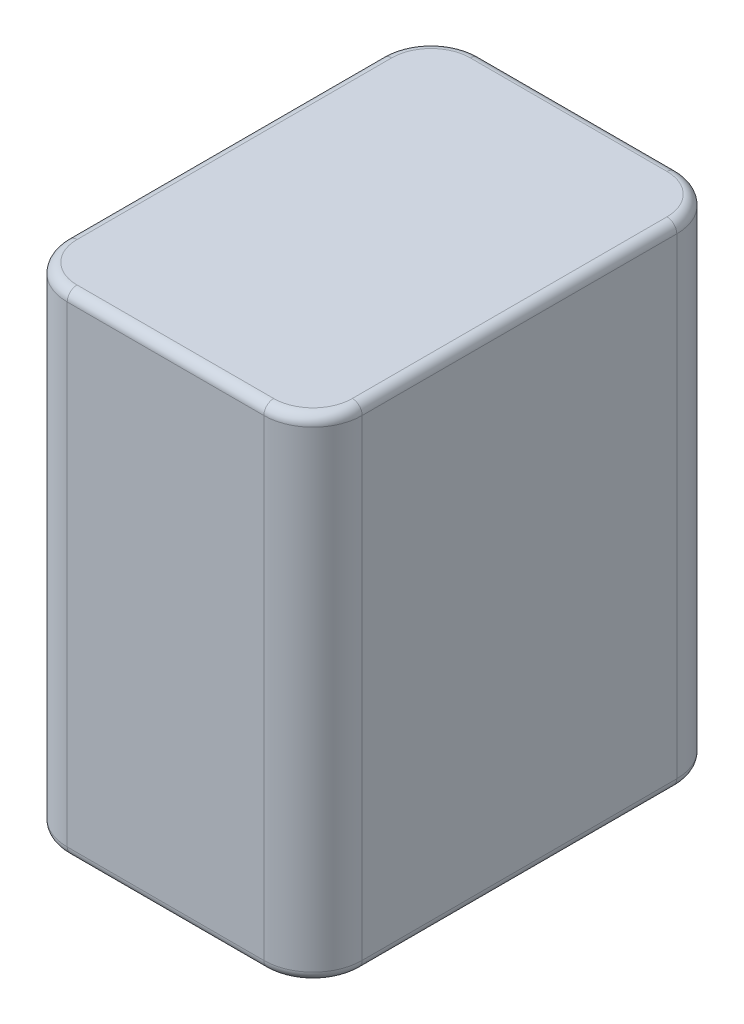
SolidWorks part; units mm, degrees
ref_plane "Front Plane" through (0, 0, 0) normal (0, 0, 1) x (1, 0, 0)
ref_plane "Top Plane" through (0, 0, 0) normal (0, 1, 0) x (1, 0, 0)
ref_plane "Right Plane" through (0, 0, 0) normal (1, 0, 0) x (0, 0, -1)
sketch "Sketch1" plane through (0, 0, 0) normal (0, 1, 0) x (1, 0, 0)
  line L1 (0, 0) -> (30, 0)
  line L2 (0, 0) -> (0, 42)
  line L3 (0, 42) -> (30, 42)
  line L4 (30, 0) -> (30, 42)
  dimension "D1" = 30
  dimension "D2" = 42
extrude "Boss-Extrude1" add sketch "Sketch1" along normal mid plane 50
fillet "Fillet1" radius 5 4 edges at (0, 0, -42) (0, 0, 0) (30, 0, -42) (30, 0, 0)
fillet "Fillet2" radius 1 8 edges at (28.5355, 25, -40.5355) (30, 25, -21) (28.5355, 25, -1.4645) (15, 25, 0) (1.4645, 25, -1.4645) (0, 25, -21) (1.4645, 25, -40.5355) (15, 25, -42)
fillet "Fillet3" radius 1 8 edges at (1.4645, -25, -1.4645) (15, -25, 0) (28.5355, -25, -1.4645) (30, -25, -21) (28.5355, -25, -40.5355) (15, -25, -42) (1.4645, -25, -40.5355) (0, -25, -21)
